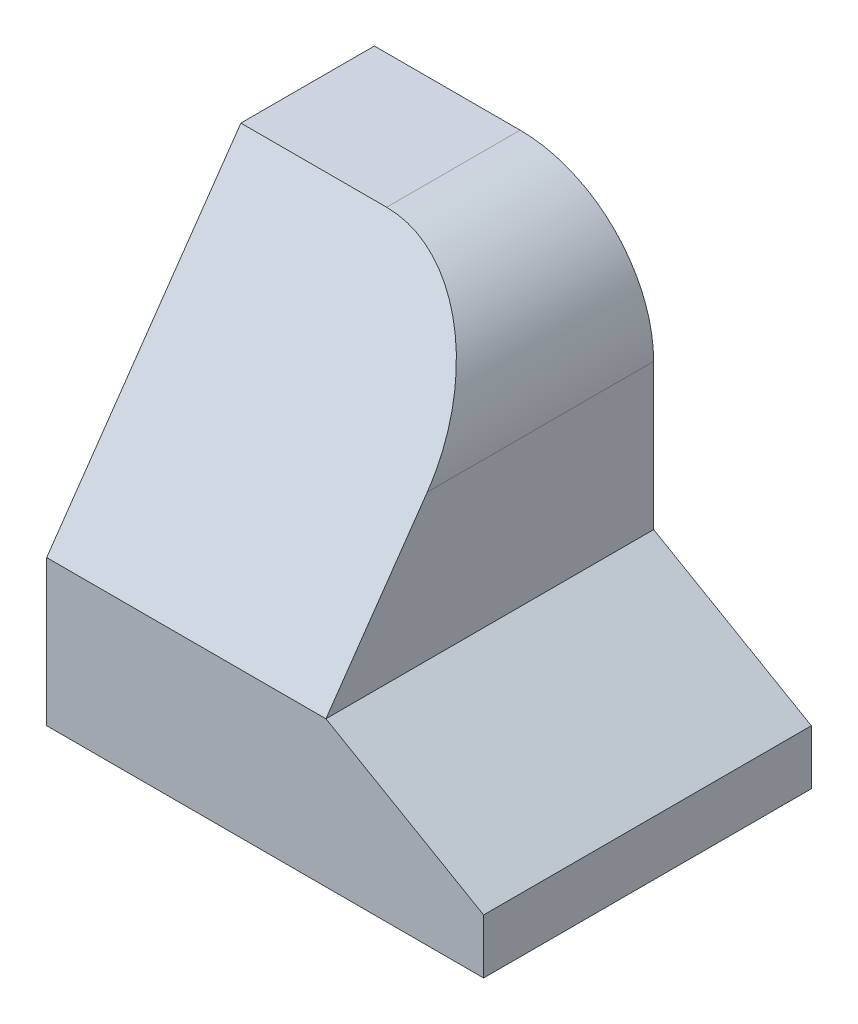
SolidWorks part; units mm, degrees
ref_plane "Front Plane" through (0, 0, 0) normal (0, 0, 1) x (1, 0, 0)
ref_plane "Top Plane" through (0, 0, 0) normal (0, 1, 0) x (1, 0, 0)
ref_plane "Right Plane" through (0, 0, 0) normal (1, 0, 0) x (0, 0, -1)
sketch "Sketch1" plane through (0, 0, 0) normal (0, 0, 1) x (1, 0, 0)
  line L0 (0, 0) -> (0, 70)
  line L1 (0, 70) -> (24.0192, 70)
  line L2 (46.0192, 48) -> (46.0192, 24)
  line L3 (46.0192, 24) -> (72, 9)
  line L4 (72, 9) -> (72, 0)
  line L5 (72, 0) -> (0, 0)
  arc A0 (46.0192, 48) -> (24.0192, 70) centre (24.0192, 48) ccw
  dimension "D3" = 24
  dimension "D6" = 22
  dimension "D1" = 9
  dimension "D2" = 120
  dimension "D4" = 72
  dimension "D5" = 70
extrude "Extrude1" add sketch "Sketch1" along normal blind 54
sketch "Sketch2" plane through (46.0192, 0, 0) normal (1, 0, 0) x (0, 0, -1)
  line L0 (-54, 24) -> (-22, 70)
  line L1 (-22, 70) -> (-54, 70)
  line L2 (-54, 70) -> (-54, 24)
  dimension "D1" = 32
extrude "Extrude2" cut sketch "Sketch2" against normal through all
